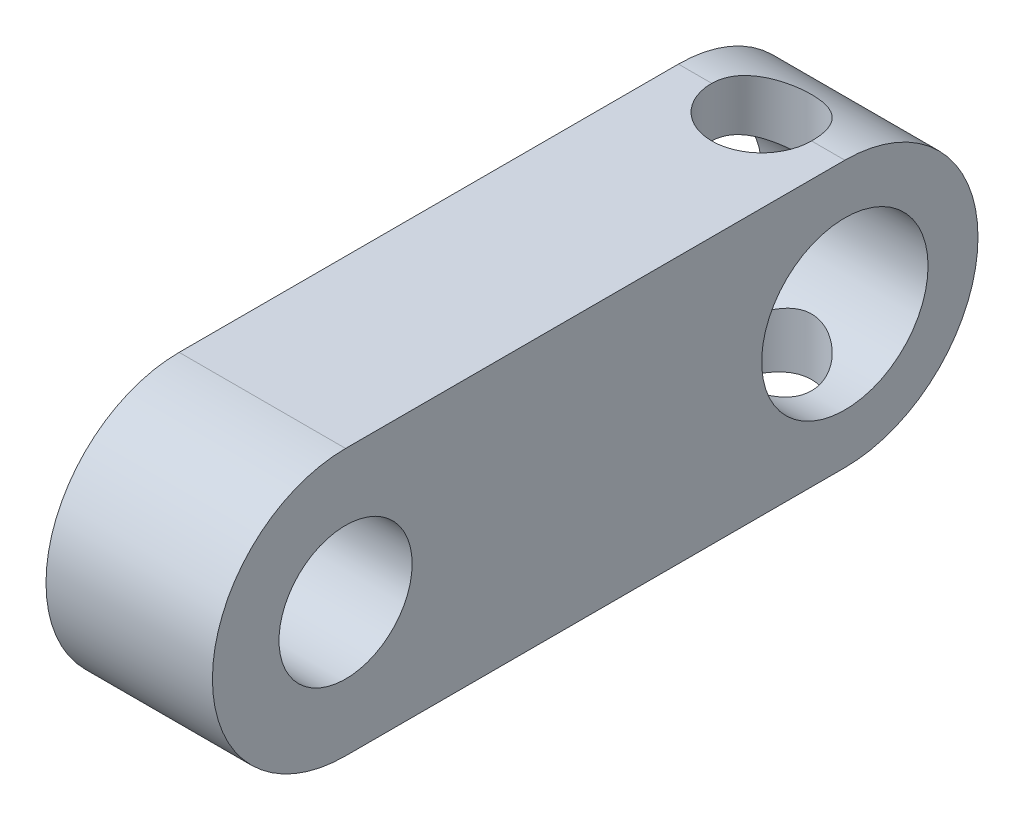
SolidWorks part; units mm, degrees
material "普通碳钢"
ref_plane "前视基准面" through (0, 0, 0) normal (0, 0, 1) x (1, 0, 0)
ref_plane "上视基准面" through (0, 0, 0) normal (0, 1, 0) x (1, 0, 0)
ref_plane "右视基准面" through (0, 0, 0) normal (1, 0, 0) x (0, 0, -1)
sketch "草图1" plane through (0, 0, 0) normal (1, 0, 0) x (0, 0, -1)
  line L0 (0, 28.2267) -> (0, -33.4957) construction
  line L1 (-74.8948, 0) -> (95.5944, 0) construction
  line L2 (15, 8) -> (-15, 8)
  line L3 (-15, -8) -> (15, -8)
  line L4 (74.8948, 0) -> (-95.5944, 0) construction
  arc A0 (-15, 8) -> (-15, -8) centre (-15, 0) ccw
  circle A1 centre (-15, 0) radius 4
  circle A2 centre (15, 0) radius 5
  arc A3 (15, 8) -> (15, -8) centre (15, 0) cw
  point P11 (0, 8)
  point P17 (0, -8)
  dimension "D1" = 8
  dimension "D2" = 8
  dimension "D4" = 10
  dimension "D3" = 30
extrude "凸台-拉伸1" add sketch "草图1" along normal blind 10
sketch3d "3D草图1"
  line L0 (-10.0611, 0, -15) -> (10, 0, -15) construction
  line L1 (10, 0, -15) -> (0, 0, -15) construction
sketch "草图2" plane through (0, 8, 0) normal (0, 1, 0) x (1, 0, 0)
  line L0 (5, 23) -> (5, 18.3538) construction
  line L1 (10, 23) -> (0, 23) construction
  line L2 (-10.0611, 15) -> (10, 15) construction
  circle A0 centre (5, 15) radius 3
  dimension "D1" = 6
extrude "切除-拉伸1" cut sketch "草图2" against normal through all
